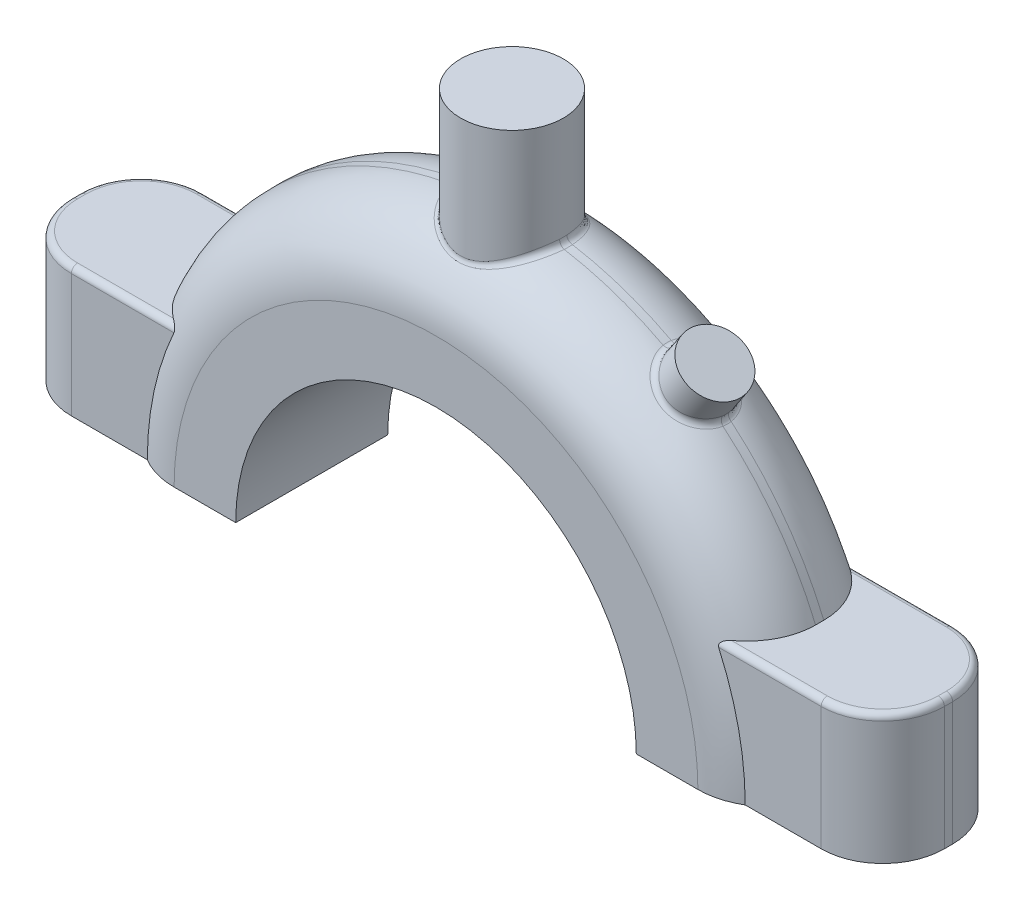
SolidWorks part; units mm, degrees
material "Malleable Cast Iron"
ref_plane "Front Plane" through (0, 0, 0) normal (0, 0, 1) x (1, 0, 0)
ref_plane "Top Plane" through (0, 0, 0) normal (0, 1, 0) x (1, 0, 0)
ref_plane "Right Plane" through (0, 0, 0) normal (1, 0, 0) x (0, 0, -1)
sketch "Sketch8" plane through (0, 0, 0) normal (0, 0, 1) x (1, 0, 0)
  line L0 (-82.55, 0) -> (0, 0) construction
  line L1 (0, 0) -> (82.55, 0) construction
  line L2 (-49.53, 0) -> (-82.55, 0)
  line L3 (49.53, 0) -> (82.55, 0)
  arc A0 (-82.55, 0) -> (82.55, 0) centre (0, 0) cw
  arc A1 (-49.53, 0) -> (49.53, 0) centre (0, 0) cw
  dimension "D1" = 49.53
  dimension "D2" = 82.55
extrude "Boss-Extrude2" add sketch "Sketch8" along normal mid plane 37.592
fillet "Fillet1" radius 17.78 2 edges at (0, 82.55, -18.796) (0, 82.55, 18.796)
sketch "Sketch9" plane through (0, 0, 0) normal (0, -1, 0) x (1, 0, 0)
  line L0 (0, 0) -> (0, 61.2588) construction
  line L1 (-177.672, 0) -> (177.672, 0) construction
  line L2 (-57.15, -16.256) -> (-107.95, -16.256)
  line L3 (57.15, 16.256) -> (107.95, 16.256)
  line L4 (57.15, 16.256) -> (57.15, -16.256)
  line L5 (57.15, -16.256) -> (107.95, -16.256)
  line L6 (107.95, 16.256) -> (107.95, -16.256)
  line L7 (57.15, 16.256) -> (107.95, -16.256) construction
  line L8 (57.15, -16.256) -> (107.95, 16.256) construction
  line L9 (-107.95, 16.256) -> (-107.95, -16.256)
  line L10 (-57.15, 16.256) -> (-107.95, 16.256)
  line L11 (-57.15, 16.256) -> (-57.15, -16.256)
  point P4 (82.55, 0)
  dimension "D1" = 215.9
  dimension "D2" = 32.512
  dimension "D3" = 50.8
extrude "Boss-Extrude3" add sketch "Sketch9" against normal blind 32.004
fillet "Fillet2" radius 15.24 4 edges at (-107.95, 16.002, -16.256) (-107.95, 16.002, 16.256) (107.95, 16.002, -16.256) (107.95, 16.002, 16.256)
sketch "Sketch10" plane through (0, 0, 0) normal (0, 0, 1) x (1, 0, 0)
  line L0 (0, 0) -> (0, 108.3563) construction
  line L1 (0, 108.3563) -> (50.1763, 74.6139) construction
  line L2 (50.1763, 74.6139) -> (0, 0) construction
  dimension "D1" = 33.92
  dimension "D2" = 89.916
ref_plane "Plane1" through (0, 108.3563, 0) normal (0, 1, 0) x (1, 0, 0)
ref_plane "Plane2" through (50.1763, 74.6139, 0) normal (-0.558, -0.8298, 0) x (-0.8298, 0.558, 0)
sketch "Sketch11" plane through (50.1763, 74.6139, 0) normal (-0.558, -0.8298, 0) x (-0.8298, 0.558, 0)
  circle A0 centre (0, 0) radius 7.62
  dimension "D1" = 15.24
extrude "Boss-Extrude4" add sketch "Sketch11" along normal blind 32.004
sketch "Sketch12" plane through (0, 108.3563, 0) normal (0, 1, 0) x (1, 0, 0)
  circle A0 centre (0, 0) radius 12.7
  dimension "D1" = 25.4
extrude "Boss-Extrude5" add sketch "Sketch12" against normal blind 32.004
fillet "Fillet3" radius 1.524 18 edges at (-79.6758, 32.004, -16.256) (-103.4863, 32.004, -11.7923) (-107.95, 32.004, 0) (-103.4863, 32.004, 11.7923) (79.6758, 32.004, -16.256) (103.4863, 32.004, -11.7923) (107.95, 32.004, 0) (103.4863, 32.004, 11.7923) (52.1568, 63.9857, 0.8321) (44.6882, 67.911, -7.5764) (-0.9426, 78.1967, -12.665) (-79.6758, 32.004, 16.256) (79.6758, 32.004, 16.256) (46.0386, 67.0029, 7.5764) (0.9426, 78.1967, 12.665)
